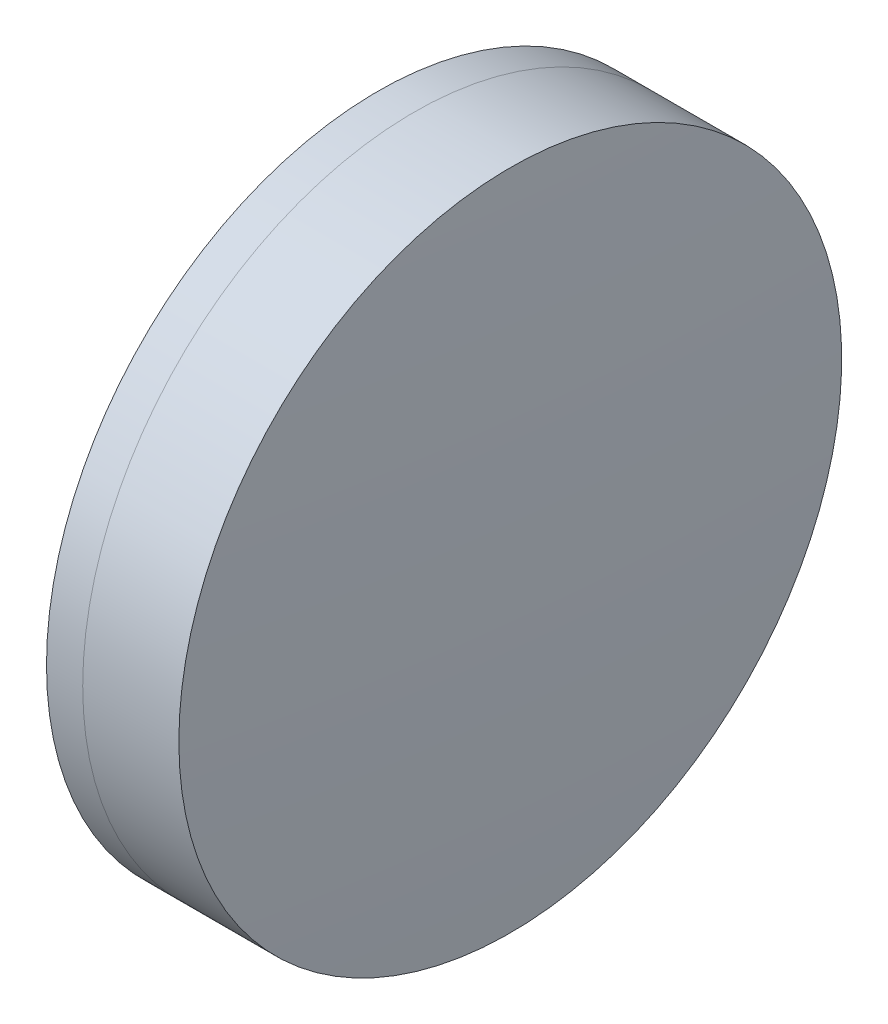
SolidWorks part; units mm, degrees
ref_plane "前视基准面" through (0, 0, 0) normal (0, 0, 1) x (1, 0, 0)
ref_plane "上视基准面" through (0, 0, 0) normal (0, 1, 0) x (1, 0, 0)
ref_plane "右视基准面" through (0, 0, 0) normal (1, 0, 0) x (0, 0, -1)
sketch "草图1" plane through (0, 0, 0) normal (0, 1, 0) x (1, 0, 0)
  line L0 (124.5233, 0) -> (646.9917, 0) construction
  line L1 (561.2099, -25.4) -> (563.9855, -25.4)
  line L2 (561.2099, 25.4) -> (563.9855, 25.4)
  arc A0 (563.9855, -25.4) -> (563.9855, 25.4) centre (457.7806, 0) ccw
  arc A1 (561.2099, 25.4) -> (561.2099, -25.4) centre (692.7806, 0) ccw
  point P10 (558.7806, 0)
  point P11 (566.9806, 0)
  dimension "D3" = 134
  dimension "D4" = 109.2
  dimension "D1" = 25.4
  dimension "D2" = 25.4
  dimension "D5" = 8.2
revolve "旋转1" add sketch "草图1" angle 360 about L0
sketch "草图2" plane through (0, 0, 0) normal (0, 1, 0) x (1, 0, 0)
  line L0 (-0.5519, 0) -> (622.6607, 0) construction
  line L2 (563.9855, 25.4) -> (571.3541, 25.4)
  line L3 (563.9855, -25.4) -> (571.3541, -25.4)
  arc A0 (571.3541, -25.4) -> (571.3541, 25.4) centre (56.7806, 0) ccw
  arc A1 (563.9855, -25.4) -> (563.9855, 25.4) centre (457.7806, 0) ccw construction
  arc A2 (563.9855, -25.4) -> (563.9855, 25.4) centre (457.7806, 0) ccw
  point P4 (566.9806, 0)
  point P8 (571.9806, 0)
  dimension "D1" = 515.2
  dimension "D2" = 5
revolve "旋转3" add sketch "草图2" angle 360 about L0
